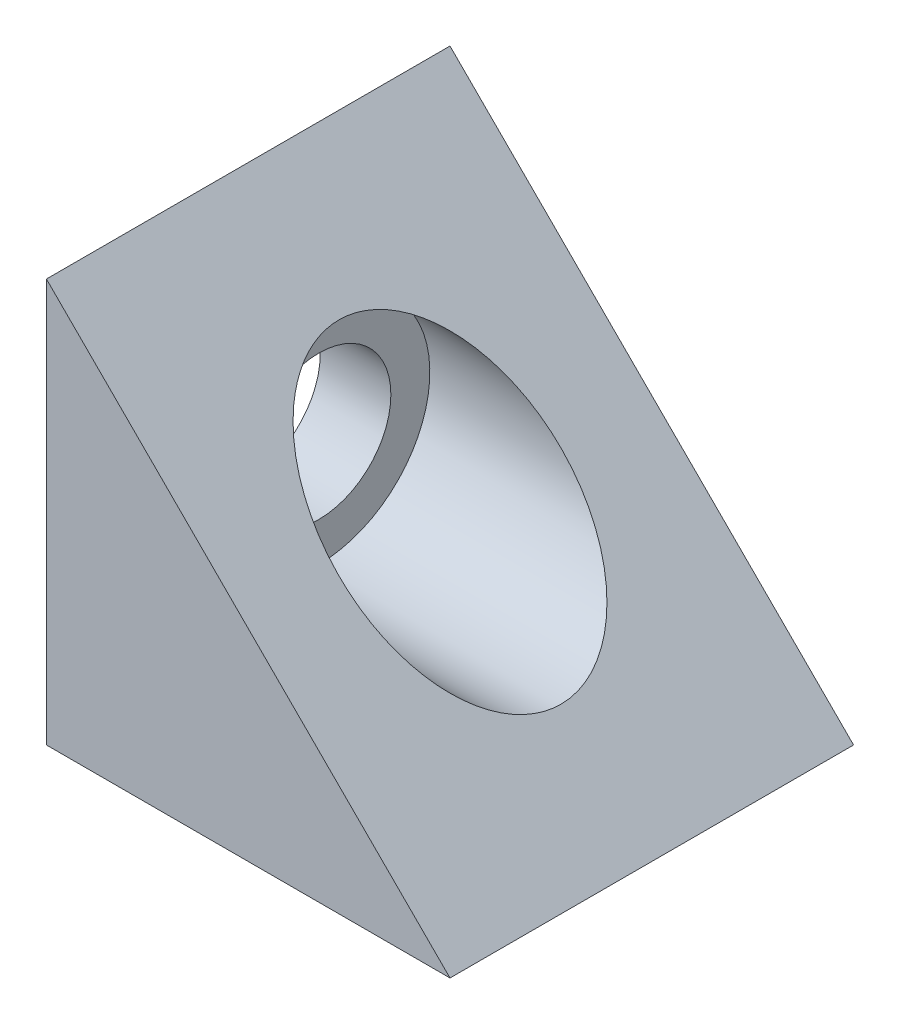
SolidWorks part; units mm, degrees
ref_plane "Front Plane" through (0, 0, 0) normal (0, 0, 1) x (1, 0, 0)
ref_plane "Top Plane" through (0, 0, 0) normal (0, 1, 0) x (1, 0, 0)
ref_plane "Right Plane" through (0, 0, 0) normal (1, 0, 0) x (0, 0, -1)
sketch "Sketch1" plane through (0, 0, 0) normal (0, 0, 1) x (1, 0, 0)
  line L0 (0, 0) -> (0, 20)
  line L1 (0, 20) -> (20, 0)
  line L2 (20, 0) -> (0, 0)
  dimension "D1" = 20
  dimension "D2" = 20
extrude "Boss-Extrude1" add sketch "Sketch1" against normal mid plane 20
ref_plane "Plane1" through (20, 0, 0) normal (1, 0, 0) x (0, 0, -1)
sketch "Sketch2" plane through (20, 0, 0) normal (1, 0, 0) x (0, 0, -1)
  line L1 (-10, 0) -> (10, 0) construction
  line L2 (-10, 0) -> (-10, 20) construction
  line L3 (-10, 20) -> (10, 20) construction
  line L4 (10, 0) -> (10, 20) construction
  circle A0 centre (0, 10) radius 3.57
  dimension "D3" = 7.14
  dimension "D1" = 20
  dimension "D2" = 20
  dimension "D4" = 10
extrude "Cut-Extrude1" cut sketch "Sketch2" against normal through all
sketch "Sketch3" plane through (20, 0, 0) normal (1, 0, 0) x (0, 0, -1)
  circle A0 centre (0, 10) radius 5.5
  point P3 (0, 0)
  dimension "D1" = 11
extrude "Cut-Extrude2" cut sketch "Sketch3" against normal offset from surface (16.5 mm away) 3.5 up to face at (0, 10, -3.57)
